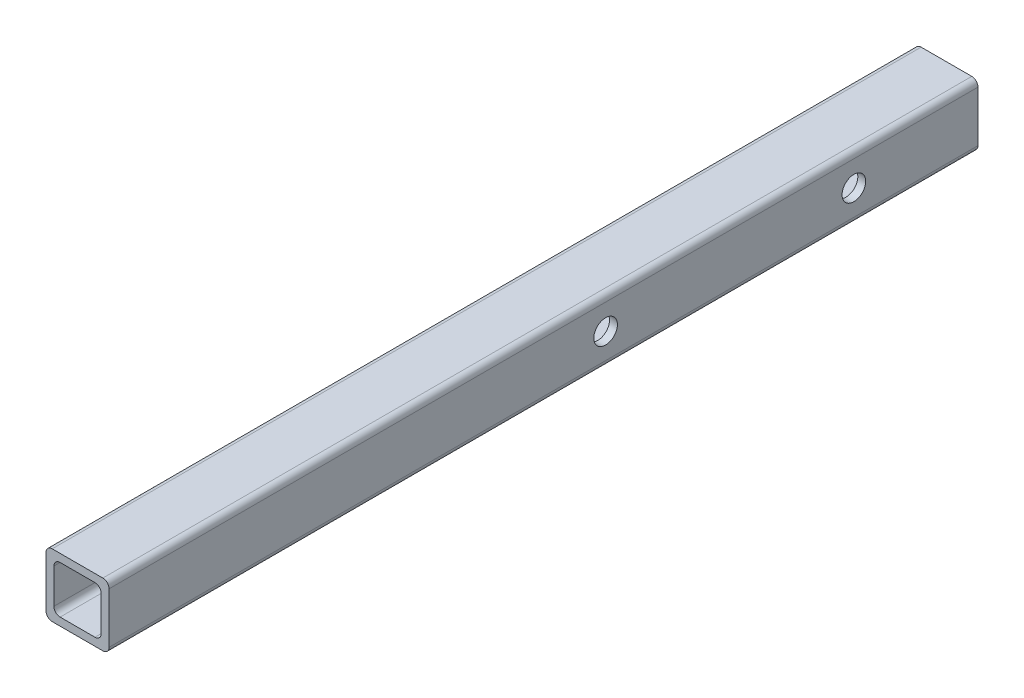
SolidWorks part; units mm, degrees
ref_plane "Alzado" through (0, 0, 0) normal (0, 0, 1) x (1, 0, 0)
ref_plane "Planta" through (0, 0, 0) normal (0, 1, 0) x (1, 0, 0)
ref_plane "Vista lateral" through (0, 0, 0) normal (1, 0, 0) x (0, 0, -1)
sketch "Croquis1" plane through (0, 0, 0) normal (0, 0, 1) x (1, 0, 0)
  line L1 (-7.025, -9.525) -> (7.025, -9.525)
  line L2 (-9.525, -7.025) -> (-9.525, 7.025)
  line L3 (-7.025, 9.525) -> (7.025, 9.525)
  line L4 (9.525, -7.025) -> (9.525, 7.025)
  line L5 (-9.525, -9.525) -> (9.525, 9.525) construction
  line L6 (-9.525, 9.525) -> (9.525, -9.525) construction
  line L7 (-10.2, -12.7) -> (10.2, -12.7)
  line L8 (-12.7, -10.2) -> (-12.7, 10.2)
  line L9 (-10.2, 12.7) -> (10.2, 12.7)
  line L10 (12.7, -10.2) -> (12.7, 10.2)
  line L11 (-12.7, -12.7) -> (12.7, 12.7) construction
  line L12 (-12.7, 12.7) -> (12.7, -12.7) construction
  arc A0 (-7.025, -9.525) -> (-9.525, -7.025) centre (-7.025, -7.025) cw
  arc A1 (7.025, -9.525) -> (9.525, -7.025) centre (7.025, -7.025) ccw
  arc A2 (9.525, 7.025) -> (7.025, 9.525) centre (7.025, 7.025) ccw
  arc A3 (12.7, -10.2) -> (10.2, -12.7) centre (10.2, -10.2) cw
  arc A4 (-10.2, -12.7) -> (-12.7, -10.2) centre (-10.2, -10.2) cw
  arc A5 (12.7, 10.2) -> (10.2, 12.7) centre (10.2, 10.2) ccw
  arc A6 (-9.525, 7.025) -> (-7.025, 9.525) centre (-7.025, 7.025) cw
  arc A7 (-10.2, 12.7) -> (-12.7, 10.2) centre (-10.2, 10.2) ccw
  point P0 (0, 0)
  point P6 (0, 0)
  dimension "D3" = 2.5
  dimension "D1" = 25.4
  dimension "D2" = 3.175
extrude "Saliente-Extruir1" add sketch "Croquis1" along normal blind 350
sketch "Croquis2" plane through (-12.7, 0, 0) normal (-1, 0, 0) x (0, 0, 1)
  circle A0 centre (50, 0) radius 4.7625
  circle A1 centre (150, 0) radius 4.7625
  dimension "D1" = 9.525
  dimension "D2" = 50
  dimension "D3" = 100
extrude "Cortar-Extruir1" cut sketch "Croquis2" against normal through all
